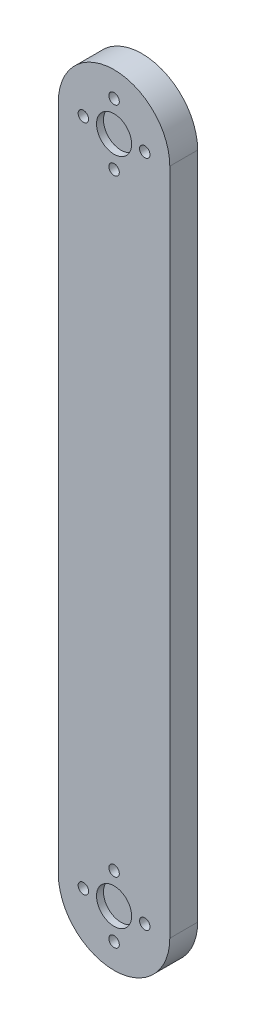
SolidWorks part; units mm, degrees
ref_plane "Front Plane" through (0, 0, 0) normal (0, 0, 1) x (1, 0, 0)
ref_plane "Top Plane" through (0, 0, 0) normal (0, 1, 0) x (1, 0, 0)
ref_plane "Right Plane" through (0, 0, 0) normal (1, 0, 0) x (0, 0, -1)
sketch "Sketch1" plane through (0, 0, 0) normal (0, 0, 1) x (1, 0, 0)
  line L0 (0, -76.2) -> (0, 76.2) construction
  line L1 (0, -55) -> (0, 55) construction
  line L2 (-12.7, -76.2) -> (-12.7, 76.2)
  line L3 (12.7, -76.2) -> (12.7, 76.2)
  arc A0 (-12.7, -76.2) -> (12.7, -76.2) centre (0, -76.2) ccw
  arc A1 (12.7, 76.2) -> (-12.7, 76.2) centre (0, 76.2) ccw
  point P5 (0, 0)
  dimension "D2" = 12.7
  dimension "D1" = 152.4
extrude "Boss-Extrude1" add sketch "Sketch1" along normal blind 6.35
sketch "Sketch2" plane through (0, 0, 6.35) normal (0, 0, 1) x (1, 0, 0)
  arc A0 (12.7, 76.2) -> (-12.7, 76.2) centre (0, 76.2) ccw construction
  arc A1 (12.7, 76.2) -> (-12.7, 76.2) centre (0, 76.2) ccw construction
  circle A2 centre (0, 76.2) radius 4
  dimension "D1" = 8
extrude "Cut-Extrude1" cut sketch "Sketch2" against normal blind 1.5875
mirror "Mirror1" about plane through (0, 0, 0) normal (0, 1, 0) of "Cut-Extrude1"
sketch "Sketch3" plane through (0, 0, 6.35) normal (0, 0, 1) x (1, 0, 0)
  circle A0 centre (0, 76.2) radius 4 construction
  circle A1 centre (0, 76.2) radius 4 construction
  circle A2 centre (0, -76.2) radius 4 construction
  circle A3 centre (0, -76.2) radius 4 construction
  circle A4 centre (0, 76.2) radius 7 construction
  circle A5 centre (0, -76.2) radius 7 construction
  circle A6 centre (0, 83.2) radius 1.1906
  circle A7 centre (0, -69.2) radius 1.1906
  dimension "D1" = 14
  dimension "D2" = 2.3813
extrude "Cut-Extrude2" cut sketch "Sketch3" against normal up to surface (6.35 mm away) up to face at (0, 0, 0)
pattern_circular "CirPattern1" count 4 over 360 about axis through (0, 76.2, 0) along (0, 0, 1) of "Cut-Extrude2"
pattern_circular "CirPattern2" count 4 over 360 about axis through (0, -76.2, 0) along (0, 0, 1) of "CirPattern1"
